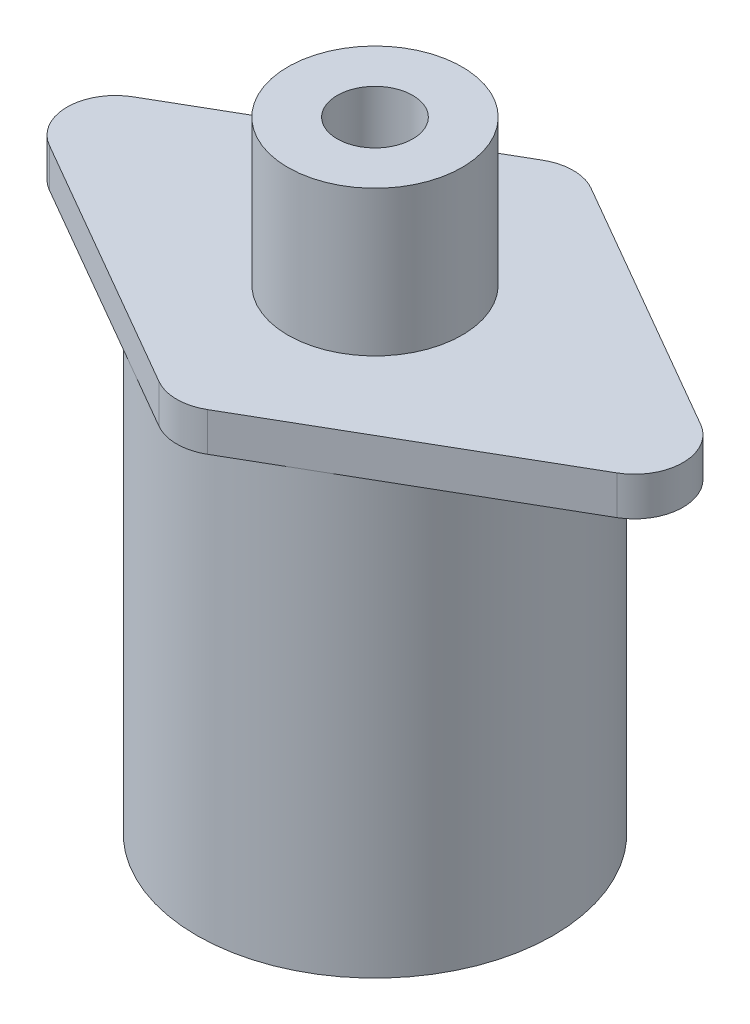
SolidWorks part; units mm, degrees
ref_plane "Alzado" through (0, 0, 0) normal (0, 0, 1) x (1, 0, 0)
ref_plane "Planta" through (0, 0, 0) normal (0, 1, 0) x (1, 0, 0)
ref_plane "Vista lateral" through (0, 0, 0) normal (1, 0, 0) x (0, 0, -1)
sketch "Sketch1" plane through (0, 0, 0) normal (0, 1, 0) x (1, 0, 0)
  circle A0 centre (0, 0) radius 18.4
  dimension "D1" = 36.8
extrude "Boss-Extrude1" add sketch "Sketch1" along normal blind 45
sketch "Sketch2" plane through (0, 45, 0) normal (0, 1, 0) x (1, 0, 0)
  line L0 (0, 21.25) -> (0, -21.25) construction
  line L1 (0, 21.25) -> (-36.8061, 0)
  line L2 (-36.8061, 0) -> (0, -21.25)
  line L3 (0, -21.25) -> (36.8061, 0)
  line L4 (36.8061, 0) -> (0, 21.25)
  dimension "D1" = 42.5
extrude "Boss-Extrude2" add sketch "Sketch2" along normal blind 4
fillet "Fillet1" radius 5 4 edges at (0, 47, -21.25) (0, 47, 21.25) (36.8061, 47, 0) (-36.8061, 47, 0)
sketch "Sketch3" plane through (0, 49, 0) normal (0, 1, 0) x (1, 0, 0)
  circle A0 centre (0, 0) radius 9
  dimension "D1" = 18
extrude "Boss-Extrude3" add sketch "Sketch3" along normal blind 15
sketch "Sketch4" plane through (0, 64, 0) normal (0, 1, 0) x (1, 0, 0)
  circle A0 centre (0, 0) radius 3.9
  dimension "D1" = 7.8
extrude "Cut-Extrude1" cut sketch "Sketch4" against normal blind 10
